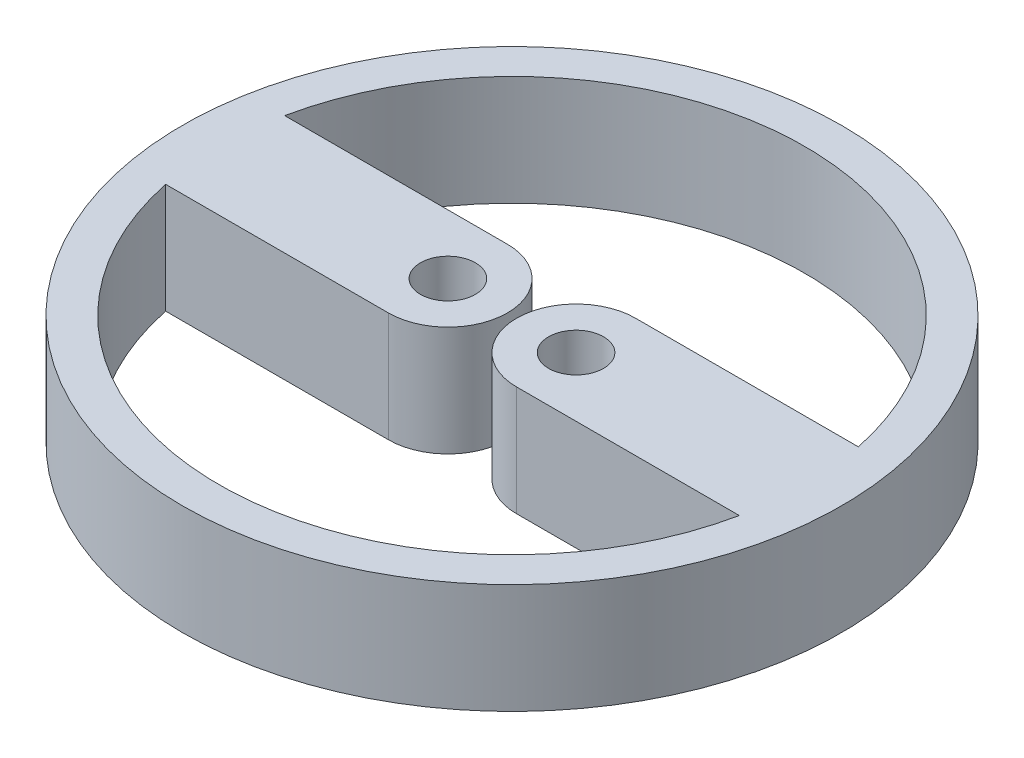
SolidWorks part; units mm, degrees
ref_plane "Plan de face" through (0, 0, 0) normal (0, 0, 1) x (1, 0, 0)
ref_plane "Plan de dessus" through (0, 0, 0) normal (0, 1, 0) x (1, 0, 0)
ref_plane "Plan de droite" through (0, 0, 0) normal (1, 0, 0) x (0, 0, -1)
sketch "Esquisse1" plane through (0, 0, 0) normal (0, 1, 0) x (1, 0, 0)
  line L0 (-3.5, 0) -> (3.5, 0) construction
  line L1 (-3.5, 3.25) -> (-15.6664, 3.25)
  line L3 (-3.5, -3.25) -> (-15.6664, -3.25)
  line L5 (3.5, 3.25) -> (15.6664, 3.25)
  line L6 (3.5, -3.25) -> (15.6664, -3.25)
  circle A0 centre (0, 0) radius 18
  circle A2 centre (-3.5, 0) radius 1.5
  circle A3 centre (3.5, 0) radius 1.5
  arc A10 (-3.5, -3.25) -> (-3.5, 3.25) centre (-3.5, 0) ccw
  arc A11 (3.5, 3.25) -> (3.5, -3.25) centre (3.5, 0) ccw
  arc A12 (-15.6664, -3.25) -> (15.6664, -3.25) centre (0, 0) ccw
  arc A13 (15.6664, 3.25) -> (-15.6664, 3.25) centre (0, 0) ccw
  dimension "D1" = 36
  dimension "D2" = 6.5
  dimension "D3" = 6.5
  dimension "D4" = 7
  dimension "D5" = 3
  dimension "D6" = 3
  dimension "D7" = 3.5
  dimension "D8" = 12.1664
  dimension "D12" = 32
extrude "Boss.-Extru.1" add sketch "Esquisse1" along normal blind 6
